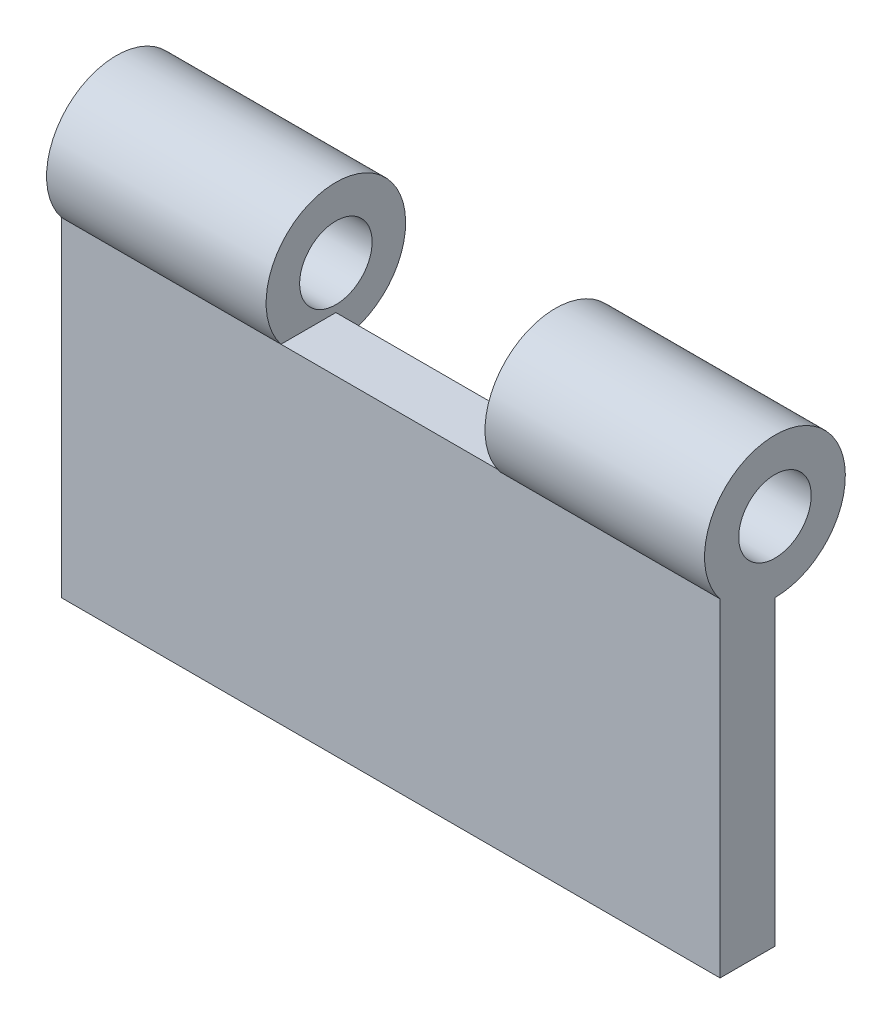
SolidWorks part; units mm, degrees
ref_plane "Front Plane" through (0, 0, 0) normal (0, 0, 1) x (1, 0, 0)
ref_plane "Top Plane" through (0, 0, 0) normal (0, 1, 0) x (1, 0, 0)
ref_plane "Right Plane" through (0, 0, 0) normal (1, 0, 0) x (0, 0, -1)
sketch "Sketch1" plane through (0, 0, 0) normal (0, 0, 1) x (1, 0, 0)
  line L1 (0, 0) -> (60, 0)
  line L2 (0, 0) -> (0, -30)
  line L3 (0, -30) -> (60, -30)
  line L4 (60, 0) -> (60, -30)
extrude "Boss-Extrude1" add sketch "Sketch1" along normal blind 5
sketch "Sketch2" plane through (60, 0, 0) normal (1, 0, 0) x (0, 0, -1)
  circle A0 centre (0, 3.9244) radius 6.4136
  circle A1 centre (0, 3.9244) radius 3.3029
extrude "Boss-Extrude2" add sketch "Sketch2" against normal blind 20
sketch "Sketch3" plane through (0, 0, 0) normal (-1, 0, 0) x (0, 0, 1)
  circle A0 centre (0, 3.9244) radius 6.3561
  circle A1 centre (0, 3.9244) radius 3.3029
extrude "Boss-Extrude3" add sketch "Sketch3" against normal blind 20
